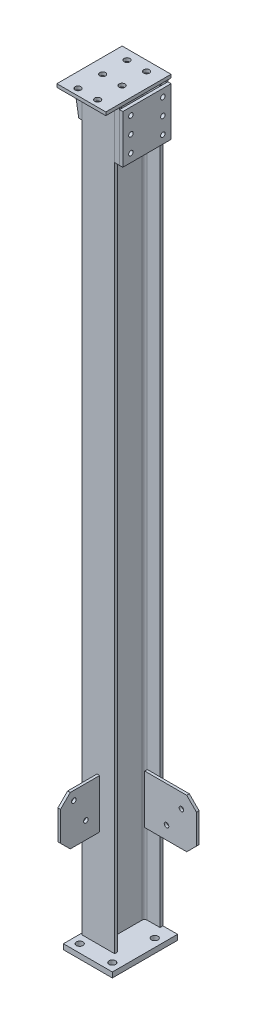
SolidWorks part; units mm, degrees
material "普通碳钢"
ref_plane "前视基准面" through (0, 0, 0) normal (0, 0, 1) x (1, 0, 0)
ref_plane "上视基准面" through (0, 0, 0) normal (0, 1, 0) x (1, 0, 0)
ref_plane "右视基准面" through (0, 0, 0) normal (1, 0, 0) x (0, 0, -1)
sketch "草图17" plane through (0, 0, 0) normal (1, 0, 0) x (0, 0, -1)
  line L0 (0, 0) -> (0, 2263)
  dimension "D1" = 2263
other "H型钢 HM150×100(7)"
ref_plane "基准面1" through (0, 0, 0) normal (0, 1, 0) x (1, 0, 0)
sketch "草图1" plane through (0, 0, 0) normal (0, 1, 0) x (1, 0, 0)
  line L0 (-50, -74) -> (50, -74)
  line L1 (50, -74) -> (50, -65)
  line L2 (50, -65) -> (11, -65)
  line L3 (3, -57) -> (3, 57)
  line L4 (11, 65) -> (50, 65)
  line L5 (50, 65) -> (50, 74)
  line L6 (50, 74) -> (-50, 74)
  line L7 (0, 74) -> (0, -74) construction
  line L11 (0, 60) -> (0, 74) construction
  line L14 (-50, -74) -> (-50, -65)
  line L15 (-50, -65) -> (-11, -65)
  line L16 (-3, -57) -> (-3, 57)
  line L17 (-11, 65) -> (-50, 65)
  line L18 (-50, 65) -> (-50, 74)
  arc A2 (11, -65) -> (3, -57) centre (11, -57) cw
  arc A3 (3, 57) -> (11, 65) centre (11, 57) cw
  arc A5 (-11, -65) -> (-3, -57) centre (-11, -57) ccw
  arc A6 (-3, 57) -> (-11, 65) centre (-11, 57) ccw
  point P2 (0, 0)
  point P38 (0, 0)
  point P39 (50, 74)
  point P40 (50, -74)
  point P41 (-50, -74)
  dimension "D8" = 8
  dimension "D1" = 6
  dimension "D2" = 9
  dimension "D3" = 148
  dimension "D4" = 100
  dimension "D9" = 0
sketch "草图18" plane through (0, 2263, 0) normal (0, 1, 0) x (1, 0, 0)
  line L1 (75, -126) -> (-75, -126)
  line L2 (75, -126) -> (75, 74)
  line L3 (75, 74) -> (-75, 74)
  line L4 (-75, -126) -> (-75, 74)
  line L5 (50, -74) -> (50, -65) construction
  line L6 (50, 74) -> (-50, 74) construction
  dimension "D1" = 200
  dimension "D2" = 150
  dimension "D3" = 25
extrude "凸台-拉伸1" add sketch "草图18" along normal blind 10 separate body contours L3 L4 L1 L2
sketch "草图19" plane through (0, 2273, 0) normal (0, 1, 0) x (1, 0, 0)
  line L0 (0, -126) -> (0, 74) construction
  line L1 (75, -126) -> (-75, -126) construction
  line L2 (75, 74) -> (-75, 74) construction
  line L3 (-75, -106) -> (75, -106) construction
  line L4 (-75, -126) -> (-75, 74) construction
  line L5 (75, -126) -> (75, 74) construction
  line L6 (-75, -31) -> (75, -31) construction
  line L7 (-75, 44) -> (75, 44) construction
  line L8 (-30, -126) -> (-30, 74) construction
  line L9 (30, -126) -> (30, 74) construction
  circle A0 centre (-30, 44) radius 9
  circle A1 centre (30, 44) radius 9
  circle A2 centre (-30, -31) radius 9
  circle A3 centre (30, -31) radius 9
  circle A4 centre (-30, -106) radius 9
  circle A5 centre (30, -106) radius 9
  dimension "D1" = 30
  dimension "D6" = 18
  dimension "D2" = 75
  dimension "D3" = 75
  dimension "D4" = 30
  dimension "D5" = 30
extrude "切除-拉伸4" cut sketch "草图19" against normal up to next (10 mm away)
sketch "草图20" plane through (0, 0, 0) normal (0, -1, 0) x (1, 0, 0)
  line L0 (-50, -74) -> (-50, -65) construction
  line L1 (-55, -74) -> (95, -74)
  line L2 (-55, -74) -> (-55, 126)
  line L3 (-55, 126) -> (95, 126)
  line L4 (95, -74) -> (95, 126)
  line L5 (50, -74) -> (-50, -74) construction
  dimension "D1" = 5
  dimension "D2" = 150
  dimension "D3" = 200
extrude "凸台-拉伸2" add sketch "草图20" along normal blind 16 separate body contours L3 L4 L1 L2
sketch "草图22" plane through (0, 0, 74) normal (0, 0, 1) x (1, 0, 0)
  line L0 (-50, 2263) -> (-50, 0) construction
  line L1 (4, 300) -> (-4, 300)
  line L2 (4, 300) -> (4, 450)
  line L3 (4, 450) -> (-4, 450)
  line L4 (-4, 300) -> (-4, 450)
  line L5 (-50, 0) -> (50, 0) construction
  dimension "D1" = 8
  dimension "D2" = 150
  dimension "D3" = 46
  dimension "D4" = 300
extrude "凸台-拉伸4" add sketch "草图22" along normal blind 120 separate body
chamfer "倒角1" distance 30 angle 45 2 edges at (0, 300, 194) (0, 450, 194)
sketch "草图23" plane through (-4, 0, 0) normal (-1, 0, 0) x (0, 0, 1)
  line L0 (191.1345, 403.1142) -> (153.0094, 422.9609) construction
  line L1 (154.1946, 332.1533) -> (116.0695, 352) construction
  line L2 (1023.6924, 2095.5275) -> (89, 300) construction
  line L3 (164, 300) -> (74, 300) construction
  line L5 (74, 450) -> (74, 300) construction
  circle A0 centre (116.0695, 352) radius 7
  circle A1 centre (153.0094, 422.9609) radius 7
  dimension "D3" = 14
  dimension "D4" = 14
  dimension "D1" = 80
  dimension "D2" = 62.5
  dimension "D5" = 52
  dimension "D6" = 15
extrude "切除-拉伸5" cut sketch "草图23" against normal up to next (8 mm away)
sketch "草图24" plane through (0, 0, -65) normal (0, 0, 1) x (1, 0, 0)
  line L0 (11, 2263) -> (11, 0) construction
  line L1 (11, 400) -> (170, 400)
  line L2 (11, 400) -> (11, 250)
  line L3 (11, 250) -> (170, 250)
  line L4 (170, 400) -> (170, 250)
  line L5 (50, 2263) -> (50, 0) construction
  line L6 (11, 0) -> (50, 0) construction
  dimension "D1" = 120
  dimension "D2" = 150
  dimension "D3" = 250
extrude "凸台-拉伸5" add sketch "草图24" along normal blind 8 separate body contours L4 L3 L2 L1
chamfer "倒角2" distance 30 angle 45 2 edges at (170, 250, -61) (170, 400, -61)
sketch "草图25" plane through (0, 0, -65) normal (0, 0, -1) x (-1, 0, 0)
  line L0 (-50, 250) -> (-164.7326, 413.8551) construction
  line L1 (-11, 250) -> (-140, 250) construction
  line L2 (-50, 2263) -> (-50, 0) construction
  line L5 (-11, 290) -> (-140, 290)
  line L6 (-11, 290) -> (-140, 290) construction
  circle A0 centre (-78.0083, 290) radius 7
  circle A1 centre (-123.8944, 355.5322) radius 7
  dimension "D3" = 14
  dimension "D4" = 14
  dimension "D1" = 55
  dimension "D5" = 80
  dimension "D2" = 40
extrude "切除-拉伸6" cut sketch "草图25" against normal up to next (8 mm away)
sketch "草图26" plane through (0, 0, 74) normal (0, 0, 1) x (1, 0, 0)
  line L0 (-50, 2263) -> (-75, 2263)
  line L1 (-75, 2263) -> (-75, 2253)
  line L2 (-75, 2253) -> (-60, 2163)
  line L3 (-60, 2163) -> (-50, 2163)
  line L4 (-50, 2263) -> (-50, 0) construction
  line L5 (-50, 2163) -> (-50, 2263)
  line L11 (-75, 2273) -> (-75, 2263) construction
  line L12 (-50, 2263) -> (50, 2263) construction
  line L13 (50, 2263) -> (50, 0) construction
  line L14 (50, 2263) -> (65, 2263)
  line L15 (50, 2263) -> (50, 2100)
  line L16 (50, 2100) -> (65, 2100)
  line L17 (65, 2263) -> (65, 2100)
  dimension "D1" = 10
  dimension "D2" = 163
  dimension "D3" = 10
  dimension "D4" = 100
  dimension "D5" = 15
extrude "凸台-拉伸6" add sketch "草图26" against normal blind 6 separate body
sketch "草图27" plane through (0, 0, -74) normal (0, 0, -1) x (-1, 0, 0)
  line L4 (-50, 2100) -> (-50, 2263)
  line L5 (-50, 2263) -> (-65, 2263)
  line L6 (-65, 2263) -> (-65, 2100)
  line L7 (-65, 2100) -> (-50, 2100)
  line L8 (-50, 2100) -> (-50, 2263)
  line L9 (-50, 2263) -> (-65, 2263)
  line L15 (50, 2263) -> (50, 2163)
  line L16 (50, 2163) -> (60, 2163)
  line L17 (60, 2163) -> (75, 2253)
  line L18 (75, 2253) -> (75, 2263)
  line L19 (75, 2263) -> (50, 2263)
  line L20 (50, 2263) -> (50, 2163)
  line L21 (50, 2163) -> (60, 2163)
  line L22 (60, 2163) -> (75, 2253)
  line L23 (75, 2253) -> (75, 2263)
  line L24 (75, 2263) -> (50, 2263)
  line L25 (-65, 2263) -> (-65, 2100)
  line L26 (-65, 2100) -> (-50, 2100)
  dimension "D1" = 0
  dimension "D2" = 0
extrude "凸台-拉伸7" add sketch "草图27" against normal blind 6 separate body
sketch "草图28" plane through (0, 0, 74) normal (0, 0, 1) x (1, 0, 0)
  line L1 (65, 2100) -> (75, 2100)
  line L2 (65, 2100) -> (65, 2248)
  line L3 (65, 2248) -> (75, 2248)
  line L4 (75, 2100) -> (75, 2248)
  dimension "D1" = 10
  dimension "D2" = 148
extrude "凸台-拉伸8" add sketch "草图28" against normal up to surface (148 mm away) separate body up to face at (57.5, 2181.5, -74)
sketch "草图29" plane through (75, 0, 0) normal (1, 0, 0) x (0, 0, -1)
  line L0 (-49, 2225) -> (-49, 2125) construction
  line L1 (-49, 2125) -> (49, 2125) construction
  line L2 (49, 2125) -> (49, 2225) construction
  line L3 (49, 2225) -> (-49, 2225) construction
  line L4 (-49, 2175) -> (49, 2175) construction
  line L5 (74, 2100) -> (-74, 2100) construction
  line L6 (74, 2100) -> (74, 2248) construction
  circle A0 centre (-49, 2225) radius 7
  circle A1 centre (49, 2225) radius 7
  circle A2 centre (49, 2175) radius 7
  circle A3 centre (-49, 2175) radius 7
  circle A4 centre (49, 2125) radius 7
  circle A5 centre (-49, 2125) radius 7
  dimension "D1" = 98
  dimension "D6" = 14
  dimension "D2" = 50
  dimension "D3" = 50
  dimension "D4" = 25
  dimension "D5" = 25
extrude "切除-拉伸7" cut sketch "草图29" against normal up to next (10 mm away) and the other way through all
sketch "草图30" plane through (0, -16, 0) normal (0, -1, 0) x (1, 0, 0)
  line L0 (70, 101) -> (-30, 101) construction
  line L1 (-30, 101) -> (-30, -29) construction
  line L2 (-30, -29) -> (70, -29) construction
  line L3 (70, -29) -> (70, 101) construction
  line L4 (-55, 126) -> (95, 126) construction
  line L5 (95, -74) -> (95, 126) construction
  circle A0 centre (70, 101) radius 10
  circle A1 centre (-30, 101) radius 10
  circle A2 centre (-30, -29) radius 10
  circle A3 centre (70, -29) radius 10
  point P6 (70, 36)
  dimension "D5" = 20
  dimension "D1" = 100
  dimension "D2" = 130
  dimension "D3" = 25
  dimension "D4" = 25
extrude "切除-拉伸8" cut sketch "草图30" against normal up to next (16 mm away)
